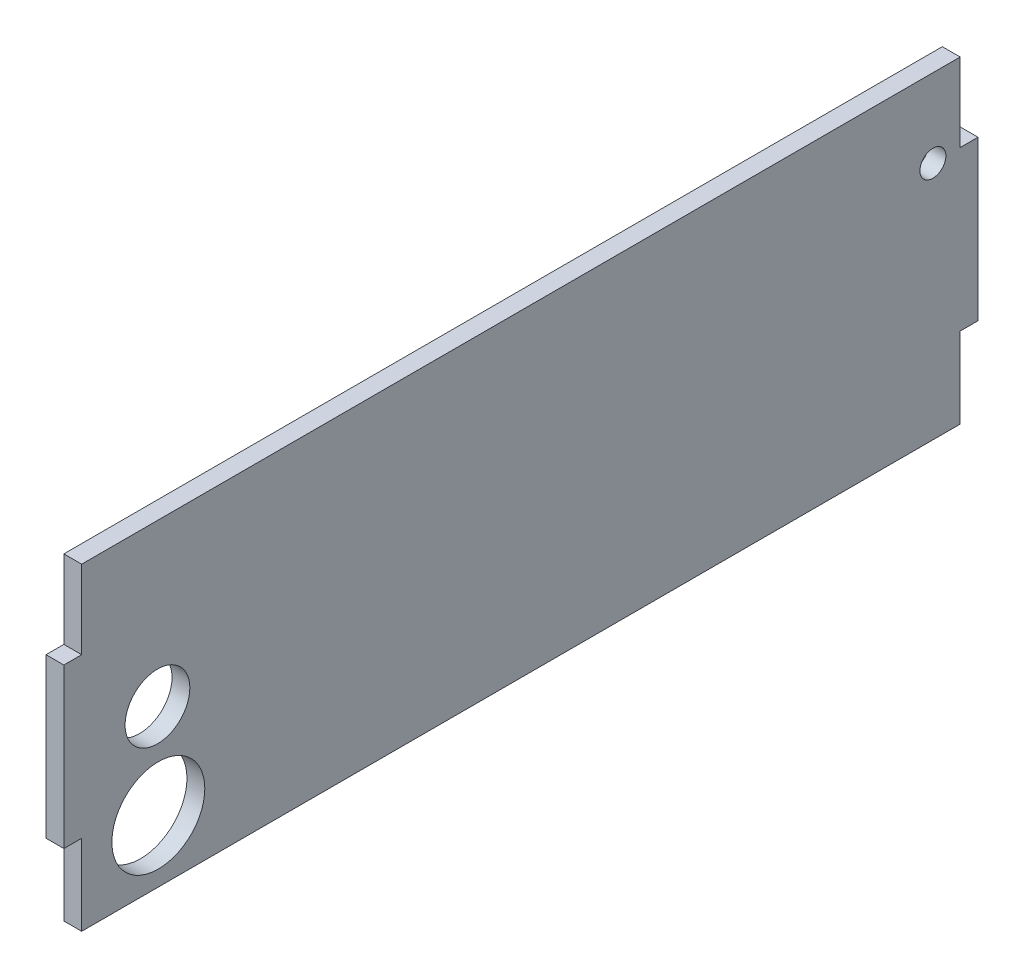
SolidWorks part; units mm, degrees
ref_plane "Front Plane" through (0, 0, 0) normal (0, 0, 1) x (1, 0, 0)
ref_plane "Top Plane" through (0, 0, 0) normal (0, 1, 0) x (1, 0, 0)
ref_plane "Right Plane" through (0, 0, 0) normal (1, 0, 0) x (0, 0, -1)
sketch "Sketch1" plane through (0, 0, 0) normal (1, 0, 0) x (0, 0, -1)
  line L0 (0, 0) -> (0, 50.8) construction
  line L7 (151.75, 25.75) -> (146.05, 25.75) construction
  line L38 (-140.35, 50.8) -> (140.35, 50.8)
  line L40 (-140.35, -50.8) -> (140.35, -50.8)
  line L45 (146.05, 25.75) -> (146.05, 50.8) construction
  line L46 (146.05, 50.8) -> (140.35, 50.8) construction
  line L47 (146.05, -25.05) -> (146.05, -50.8) construction
  line L48 (146.05, -50.8) -> (140.35, -50.8) construction
  line L58 (151.75, 25.75) -> (151.75, -25.05) construction
  line L59 (151.75, -25.05) -> (146.05, -25.05) construction
  line L60 (-140.35, 50.8) -> (-140.35, 25.75)
  line L61 (-140.35, 25.75) -> (-146.05, 25.75)
  line L62 (-146.05, 25.75) -> (-146.05, -25.05)
  line L63 (-146.05, -25.05) -> (-140.35, -25.05)
  line L64 (-140.35, -25.05) -> (-140.35, -50.8)
  line L65 (140.35, 50.8) -> (140.35, 25.75)
  line L66 (140.35, 25.75) -> (146.05, 25.75)
  line L67 (146.05, 25.75) -> (146.05, -25.05)
  line L68 (146.05, -25.05) -> (140.35, -25.05)
  line L69 (140.35, -25.05) -> (140.35, -50.8)
  circle A0 centre (131.6424, 25.75) radius 4.15
  circle A1 centre (-116.1337, -0.688) radius 10.3454
  circle A2 centre (-115.8585, -30.9598) radius 14.85
  point P0 (0, 0)
  point P27 (0, -50.8)
  dimension "D1" = 8.3
  dimension "D2" = 29.7
extrude "Boss-Extrude1" add sketch "Sketch1" along normal blind 5.7
